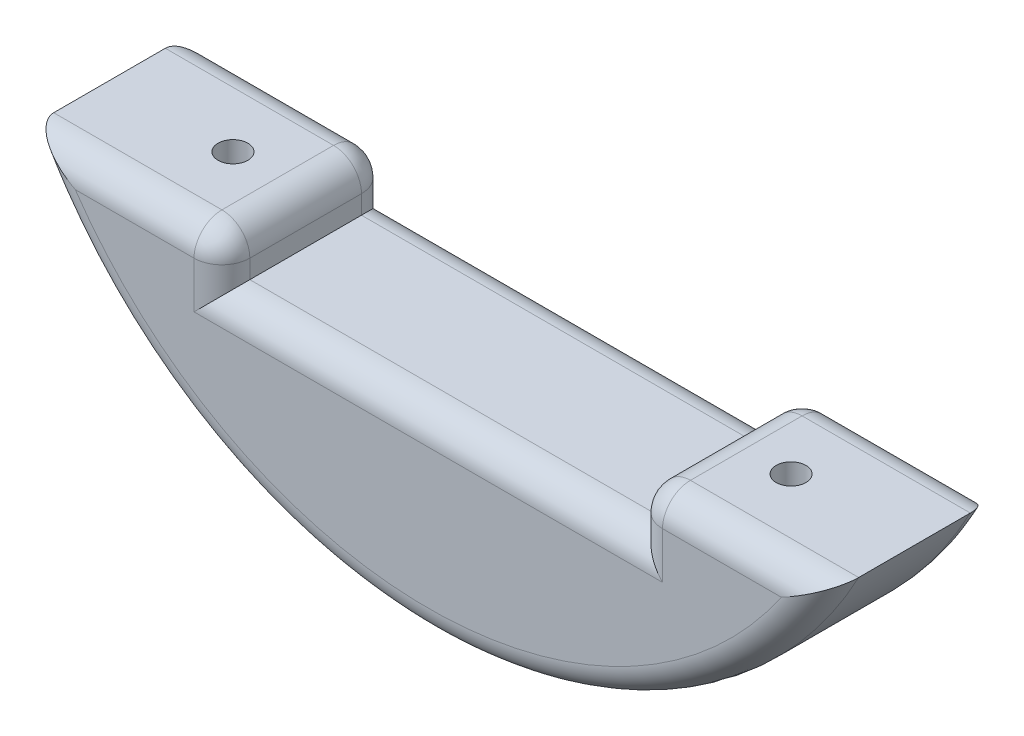
SolidWorks part; units mm, degrees
material "Pure Lead"
ref_plane "Front Plane" through (0, 0, 0) normal (0, 0, 1) x (1, 0, 0)
ref_plane "Top Plane" through (0, 0, 0) normal (0, 1, 0) x (1, 0, 0)
ref_plane "Right Plane" through (0, 0, 0) normal (1, 0, 0) x (0, 0, -1)
sketch "Sketch1" plane through (0, 0, 0) normal (0, 0, 1) x (1, 0, 0)
  line L0 (-46.6476, -15) -> (46.6476, -15)
  line L1 (-43.2666, -23) -> (43.2666, -23)
  line L2 (-33.9411, -28) -> (33.9411, -28)
  line L3 (-22.1811, -38) -> (-22.1811, -23)
  line L4 (-29.9539, -23) -> (-37.51, -23)
  line L5 (22.1811, -38) -> (22.1811, -23)
  line L6 (-22.1811, -38) -> (22.1811, -38)
  circle A0 centre (0, 0) radius 49
  circle A1 centre (0, 0) radius 44
  dimension "D1" = 8
  dimension "D2" = 98
  dimension "D3" = 88
  dimension "D4" = 15
  dimension "D5" = 5
  dimension "D8" = 10
extrude "Boss-Extrude1" add sketch "Sketch1" along normal blind 18 contours L1 A1 L2 L3 | A1 L1 A0 | L2 A1 L3 | L5 A1 L2 | L2 A1 L1 L5 | L3 L6 L5 L2 | L6 A1
sketch "Sketch2" plane through (0, -23, 0) normal (0, 1, 0) x (1, 0, 0)
  line L0 (-43.2666, -18) -> (-43.2666, 0) construction
  line L2 (-22.1811, -18) -> (-22.1811, 0) construction
  circle A1 centre (-29.9966, -9) radius 1.6
  point P6 (-22.1811, -9)
  dimension "D1" = 0
  dimension "D4" = 13.27
extrude "Cut-Extrude1" cut sketch "Sketch2" against normal through all
sketch "Sketch3" plane through (0, -23, 0) normal (0, 1, 0) x (1, 0, 0)
  circle A1 centre (-29.9966, -9) radius 3.05
extrude "Cut-Extrude2" cut sketch "Sketch3" along normal up to surface (20 mm away) from offset 25
mirror "Mirror1" about plane through (0, 0, 0) normal (1, 0, 0) of "Cut-Extrude2", "Cut-Extrude1"
fillet "Fillet1" radius 3 14 edges at (0, -28, 18) (0, -28, 0) (22.1811, -25.5, 0) (22.1811, -23, 9) (-22.1811, -23, 9) (-22.1811, -25.5, 18) (-32.7238, -23, 18) (0, -49, 18) (32.7238, -23, 18) (22.1811, -25.5, 18) (32.7238, -23, 0) (0, -49, 0) (-32.7238, -23, 0) (-22.1811, -25.5, 0)
